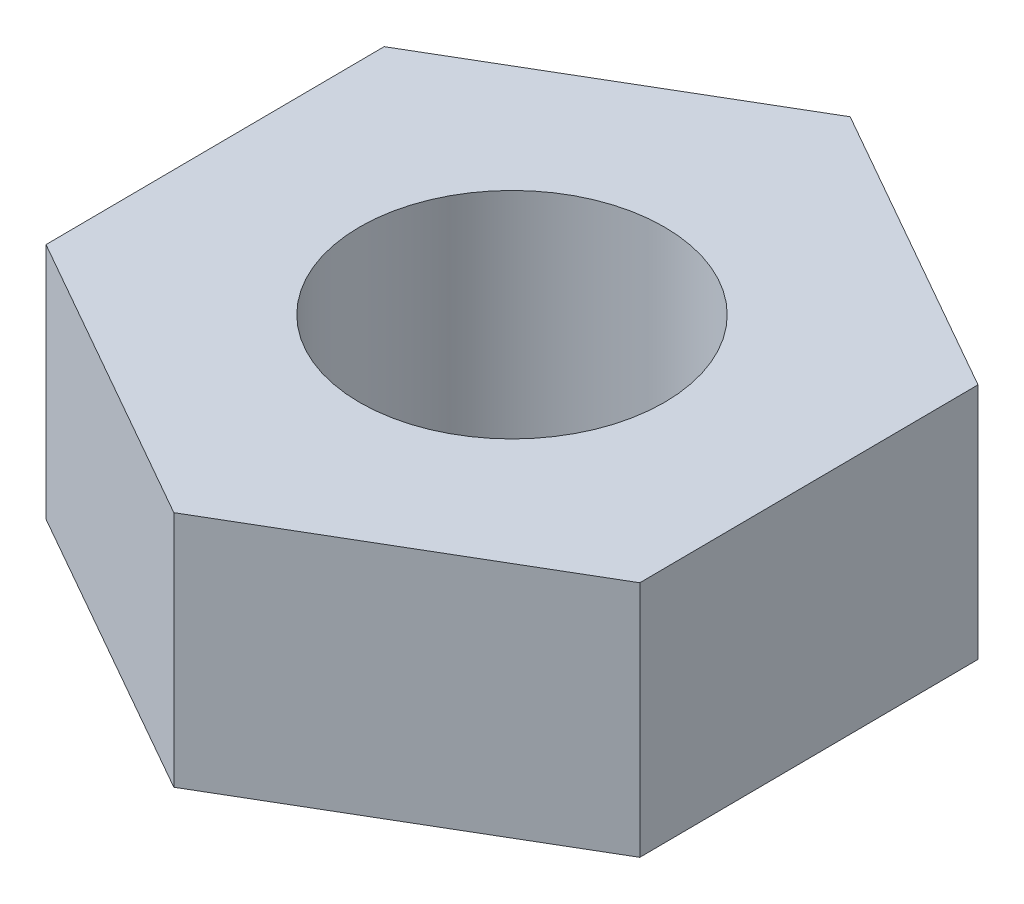
SolidWorks part; units mm, degrees
ref_plane "Front Plane" through (0, 0, 0) normal (0, 0, 1) x (1, 0, 0)
ref_plane "Top Plane" through (0, 0, 0) normal (0, 1, 0) x (1, 0, 0)
ref_plane "Right Plane" through (0, 0, 0) normal (1, 0, 0) x (0, 0, -1)
sketch "Sketch1" plane through (0, 0, 0) normal (0, 1, 0) x (1, 0, 0)
  line L1 (3.8595, 2.2639) -> (-0.0309, 4.4744)
  line L2 (-0.0309, 4.4744) -> (-3.8904, 2.2104)
  line L3 (-3.8904, 2.2104) -> (-3.8595, -2.2639)
  line L4 (-3.8595, -2.2639) -> (0.0309, -4.4744)
  line L5 (0.0309, -4.4744) -> (3.8904, -2.2104)
  line L6 (3.8904, -2.2104) -> (3.8595, 2.2639)
  circle A0 centre (0, 0) radius 3.875 construction
  circle A1 centre (0, 0) radius 2
extrude "Extrude1" add sketch "Sketch1" along normal blind 3.125
